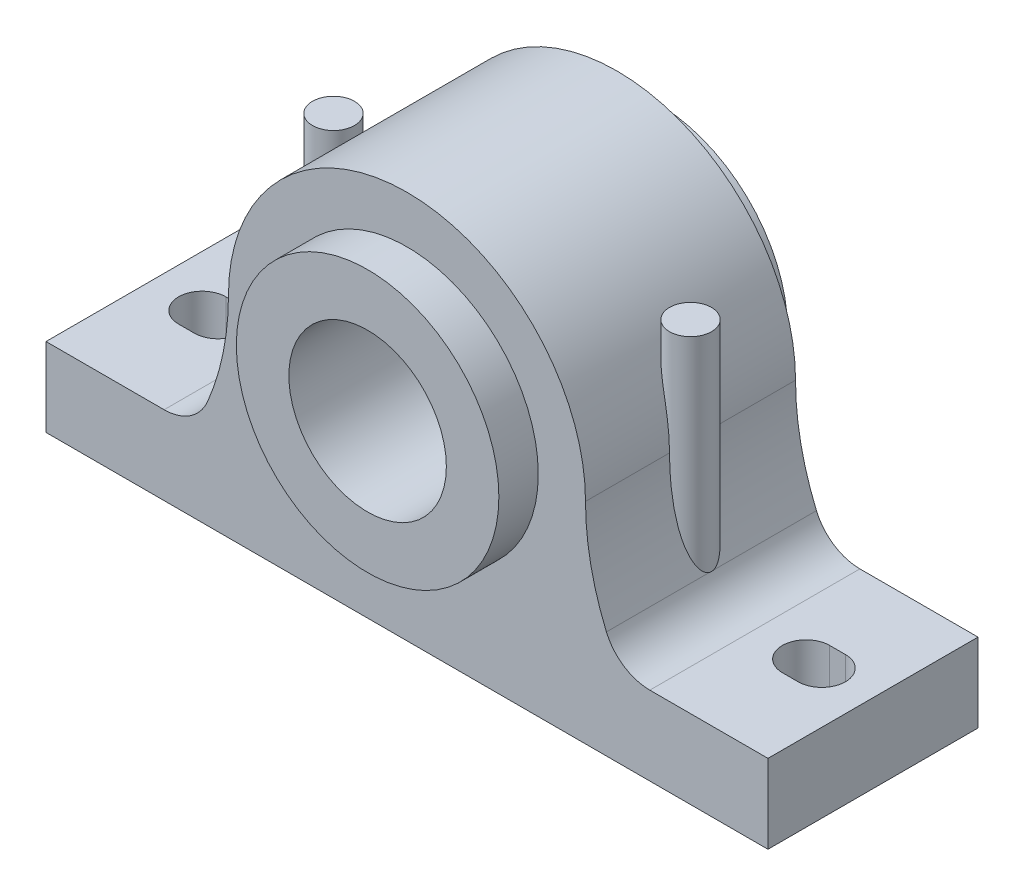
SolidWorks part; units mm, degrees
material "Plain Carbon Steel"
ref_plane "Front Plane" through (0, 0, 0) normal (0, 0, 1) x (1, 0, 0)
ref_plane "Top Plane" through (0, 0, 0) normal (0, 1, 0) x (1, 0, 0)
ref_plane "Right Plane" through (0, 0, 0) normal (1, 0, 0) x (0, 0, -1)
sketch "Sketch1" plane through (0, 0, 0) normal (0, 0, 1) x (1, 0, 0)
  line L0 (0, 72.9197) -> (0, -80) construction
  line L1 (137.5, -80) -> (-137.5, -80)
  line L2 (-137.5, -80) -> (-137.5, -50)
  line L3 (-137.5, -50) -> (-92.5, -50)
  line L4 (-115, -54.5123) -> (-115, -80) construction
  line L5 (137.5, -50) -> (92.5, -50)
  line L6 (137.5, -80) -> (137.5, -50)
  circle A0 centre (0, 0) radius 30
  arc A1 (-92.5, -50) -> (-75.9619, -39.0622) centre (-92.5, -32.0281) ccw
  arc A2 (-75.9619, -39.0622) -> (-68, 0) centre (-167.8036, 0) ccw
  arc A3 (-68, 0) -> (68, 0) centre (0, 0) cw
  arc A4 (92.5, -50) -> (75.9619, -39.0622) centre (92.5, -32.0281) cw
  arc A5 (75.9619, -39.0622) -> (68, 0) centre (167.8036, 0) cw
  point P17 (-115, -50)
  dimension "D1" = 60
  dimension "D5" = 68
  dimension "D2" = 80
  dimension "D3" = 137.5
  dimension "D4" = 115
  dimension "D6" = 30
extrude "Boss-Extrude1" add sketch "Sketch1" along normal mid plane 80
sketch "Sketch2" plane through (0, 0, 0) normal (0, 0, 1) x (1, 0, 0)
  circle A0 centre (0, 0) radius 30
  circle A1 centre (0, 0) radius 50
  dimension "D1" = 60
  dimension "D2" = 100
extrude "Boss-Extrude2" add sketch "Sketch2" along normal mid plane 110
sketch "Sketch3" plane through (0, 0, 0) normal (0, 1, 0) x (1, 0, 0)
  line L0 (0, 0) -> (-137.5, 0) construction
  line L1 (-137.5, -40) -> (-137.5, 40) construction
  line L2 (0, 0) -> (0, 72.131) construction
  line L3 (-118, 0) -> (-112, 0) construction
  line L4 (-118, 9) -> (-112, 9)
  line L5 (-118, -9) -> (-112, -9)
  line L6 (118, 0) -> (112, 0) construction
  line L7 (118, 9) -> (112, 9)
  line L8 (118, -9) -> (112, -9)
  arc A0 (-118, 9) -> (-118, -9) centre (-118, 0) ccw
  arc A1 (-112, -9) -> (-112, 9) centre (-112, 0) ccw
  arc A2 (118, 9) -> (118, -9) centre (118, 0) cw
  arc A3 (112, -9) -> (112, 9) centre (112, 0) cw
  point P8 (-115, 0)
  point P15 (115, 0)
  dimension "D2" = 115
  dimension "D1" = 18
extrude "Cut-Extrude1" cut sketch "Sketch3" against normal blind 110
sketch "Sketch5" plane through (0, 0, 0) normal (0, 1, 0) x (1, 0, 0)
  line L0 (-68, -40) -> (-68, 40) construction
  line L1 (68, -40) -> (68, 40) construction
  circle A0 centre (-68, 0) radius 8
  circle A1 centre (68, 0) radius 8
  dimension "D1" = 16
  dimension "D2" = 16
extrude "Boss-Extrude3" add sketch "Sketch5" along normal blind 40 and the other way blind 60
